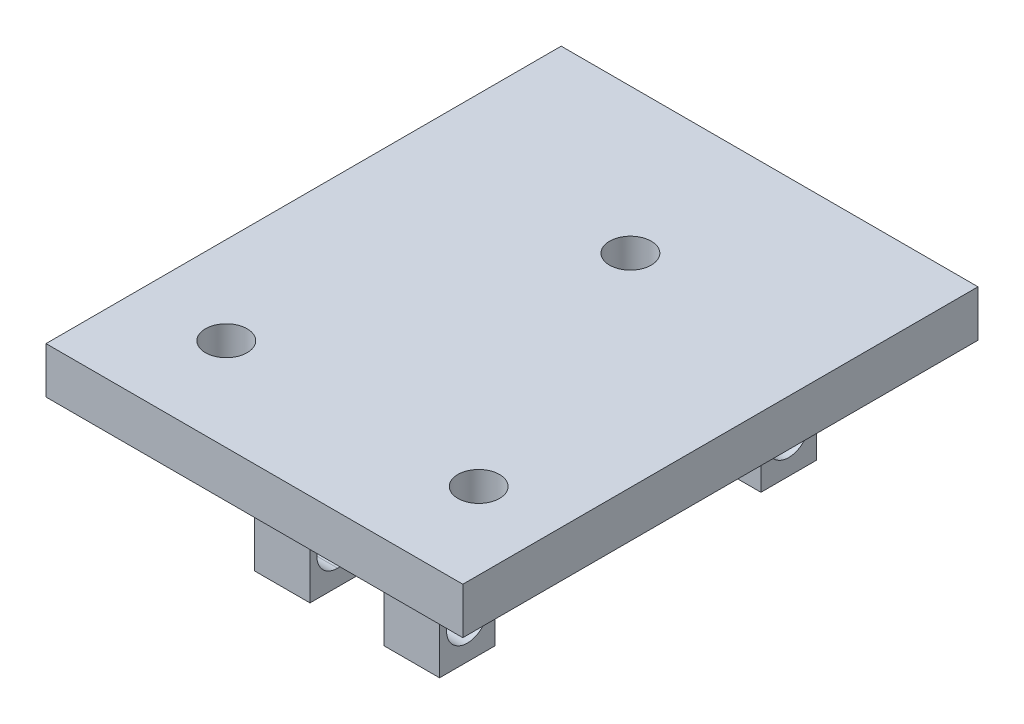
SolidWorks part; units mm, degrees
ref_plane "Front Plane" through (0, 0, 0) normal (0, 0, 1) x (1, 0, 0)
ref_plane "Top Plane" through (0, 0, 0) normal (0, 1, 0) x (1, 0, 0)
ref_plane "Right Plane" through (0, 0, 0) normal (1, 0, 0) x (0, 0, -1)
sketch "Sketch1" plane through (0, 0, 0) normal (0, 1, 0) x (1, 0, 0)
  line L0 (-14.339, 0) -> (30.661, 0)
  line L3 (8.161, 55.6215) -> (30.661, 55.6215)
  line L4 (30.661, 55.6215) -> (30.661, 0)
  line L5 (8.161, 55.6215) -> (-14.339, 55.6215)
  line L6 (-14.339, 55.6215) -> (-14.339, 0)
  dimension "D1" = 45
extrude "Boss-Extrude1" add sketch "Sketch1" along normal blind 5
hole_wizard "#8 Clearance Hole1" positions "3DSketch1" profile "Sketch2" hole size "#8" standard "ANSI Inch"
sketch3d "3DSketch1"
  line L0 (-14.339, 0, 0) -> (30.661, 0, 0) construction
  point P0 (22.3778, 0, -10)
  point P2 (-4.8722, 0, -10)
  point P4 (8.7528, 0, -40.001)
  dimension "D1" = 27.25
  dimension "D2" = 10
  dimension "D3" = 10
  dimension "D6" = 32.95
  dimension "D7" = 32.95
sketch "Sketch2" plane through (22.3778, 0, -10) normal (1, 0, 0) x (0, 0, -1)
  line L0 (0, 0) -> (0, 18.3507)
  line L1 (0, 18.3507) -> (2.2479, 17)
  line L2 (2.2479, 17) -> (2.2479, 0)
  line L5 (2.2479, 0) -> (0, 0)
  line L10 (0, 18.3507) -> (-2.2479, 17) construction
  line L11 (0, -6.35) -> (0, 107.95) construction
  dimension "Hole Dia." = 4.4958
  dimension "Hole Depth" = 17
  dimension "Drill Angle" = 118
sketch "Sketch3" plane through (0, 0, 0) normal (0, -1, 0) x (-1, 0, 0)
  line L0 (14.339, 55.6215) -> (14.339, 0) construction
  line L1 (1.839, 50.5) -> (-4.161, 50.5)
  line L2 (1.839, 50.5) -> (1.839, 44.5)
  line L3 (1.839, 44.5) -> (-4.161, 44.5)
  line L4 (-4.161, 50.5) -> (-4.161, 44.5)
  line L5 (1.839, 16) -> (-4.161, 16)
  line L6 (1.839, 16) -> (1.839, 10)
  line L7 (1.839, 10) -> (-4.161, 10)
  line L8 (-4.161, 16) -> (-4.161, 10)
  line L9 (-12.161, 50.6846) -> (-18.161, 50.6846)
  line L10 (14.339, 0) -> (-30.661, 0) construction
  line L11 (-12.161, 50.6846) -> (-12.161, 44.6846)
  line L12 (-12.161, 44.6846) -> (-18.161, 44.6846)
  line L13 (-18.161, 50.6846) -> (-18.161, 44.6846)
  line L14 (-12.161, 15.9902) -> (-18.161, 15.9902)
  line L15 (-12.161, 15.9902) -> (-12.161, 9.9902)
  line L16 (-12.161, 9.9902) -> (-18.161, 9.9902)
  line L17 (-18.161, 15.9902) -> (-18.161, 9.9902)
  line L18 (-30.661, 0) -> (-30.661, 55.6215) construction
  point P20 (0, 0)
  dimension "D1" = 34.5
  dimension "D2" = 6
  dimension "D3" = 6
  dimension "D4" = 6
  dimension "D5" = 6
  dimension "D6" = 12.5
  dimension "D7" = 6
  dimension "D8" = 10
  dimension "D9" = 6
  dimension "D10" = 8
  dimension "D11" = 6
  dimension "D12" = 6
  dimension "D13" = 8
  dimension "D14" = 12.5
extrude "Boss-Extrude2" add sketch "Sketch3" along normal blind 15
hole_wizard "#8 Clearance Hole2" positions "3DSketch2" profile "Sketch16" hole size "#8" standard "ANSI Inch"
sketch3d "3DSketch2"
  line L0 (-1.839, -15, -50.5) -> (-1.839, 0, -50.5) construction
  line L1 (-1.839, -15, -16) -> (-1.839, 0, -16) construction
  line L2 (-1.839, -15, -44.5) -> (-1.839, -15, -50.5) construction
  line L3 (-1.839, -15, -10) -> (-1.839, -15, -16) construction
  line L4 (18.161, -15, -50.6846) -> (18.161, -15, -44.6846) construction
  line L5 (18.161, -15, -50.6846) -> (18.161, 0, -50.6846) construction
  line L6 (18.161, -15, -9.9902) -> (18.161, 0, -9.9902) construction
  line L7 (18.161, -15, -15.9902) -> (18.161, -15, -9.9902) construction
  point P0 (-1.839, -11, -47.5)
  point P2 (-1.839, -11, -13)
  point P14 (18.161, -11, -47.6846)
  point P22 (18.161, -11, -12.9902)
  dimension "D1" = 3
  dimension "D2" = 3
  dimension "D3" = 4
  dimension "D4" = 4
  dimension "D5" = 4
  dimension "D6" = 3
  dimension "D7" = 3
  dimension "D8" = 4
sketch "Sketch16" plane through (-1.839, -11, -47.5) normal (0, 1, 0) x (0, 0, 1)
  line L0 (0, 0) -> (0, 18.3507)
  line L1 (0, 18.3507) -> (2.2479, 17)
  line L2 (2.2479, 17) -> (2.2479, 0)
  line L5 (2.2479, 0) -> (0, 0)
  line L10 (0, 18.3507) -> (-2.2479, 17) construction
  line L11 (0, -6.35) -> (0, 107.95) construction
  dimension "Hole Dia." = 4.4958
  dimension "Hole Depth" = 17
  dimension "Drill Angle" = 118
